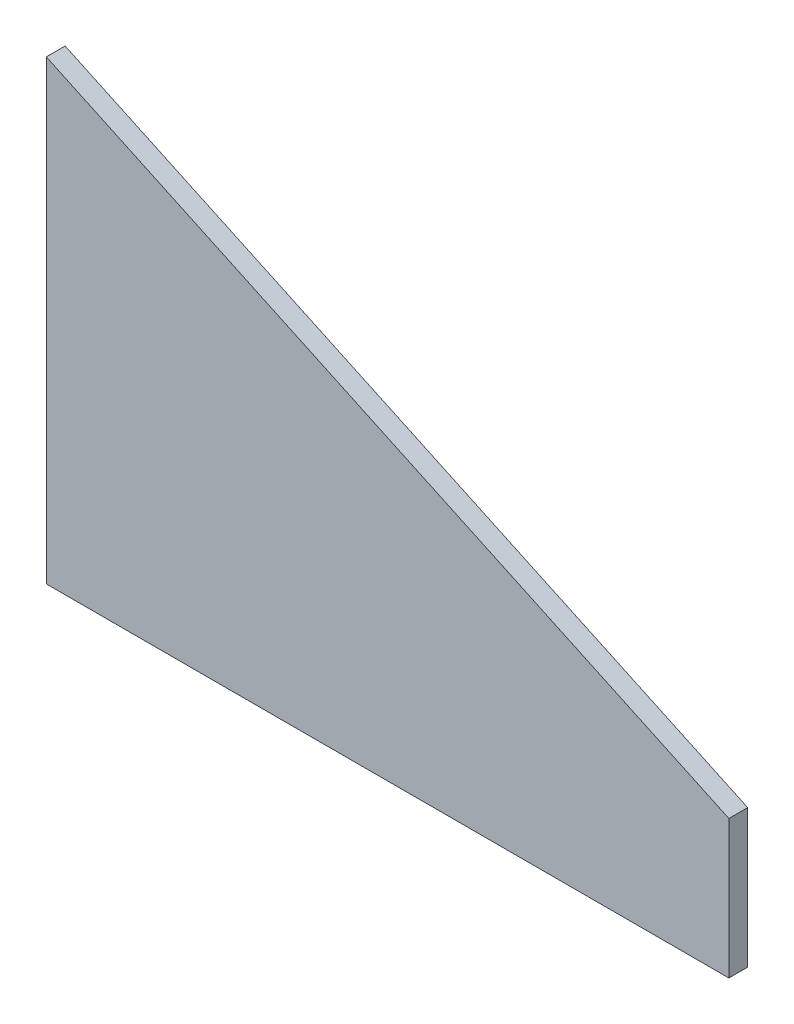
SolidWorks part; units mm, degrees
ref_plane "Front Plane" through (0, 0, 0) normal (0, 0, 1) x (1, 0, 0)
ref_plane "Top Plane" through (0, 0, 0) normal (0, 1, 0) x (1, 0, 0)
ref_plane "Right Plane" through (0, 0, 0) normal (1, 0, 0) x (0, 0, -1)
sketch "Sketch1" plane through (0, 0, 0) normal (0, 0, 1) x (1, 0, 0)
  line L0 (0, 0) -> (230.2022, 0)
  line L1 (230.2022, 0) -> (230.2022, 46.5901)
  line L2 (230.2022, 46.5901) -> (0, 153.9351)
  line L3 (0, 153.9351) -> (0, 0)
  line L4 (118.0552, 46.5901) -> (50118.0552, 46.5901) construction
  line L5 (48.3053, 131.41) -> (94.3457, 109.941) construction
  line L6 (94.3457, 109.941) -> (46.0404, 6.35) construction
  line L7 (46.0404, 6.35) -> (0, 27.819) construction
  line L8 (0, 27.819) -> (48.3053, 131.41) construction
  point P7 (-25.3116, 10.0219)
  point P12 (46.0404, 90.9538)
  point P13 (46.0404, 0)
  point P14 (46.0404, 73.325)
  point P15 (-42.5397, 18.0349)
  point P16 (-38.9338, 40.4715)
  point P17 (158.1874, 0)
  point P18 (0, 185.5078)
  point P19 (62.1589, 148.2151)
  point P20 (230.2022, 120.5219)
  point P21 (230.2022, 0)
  point P22 (0.0235, 261.2953)
  point P23 (4.7525, 273.6418)
  point P24 (0, 0)
  point P25 (0, 0)
  point P26 (230.2022, 249.2911)
  point P27 (48.3053, 9.0354)
  dimension "D1" = 25
  dimension "D2" = 114.3
  dimension "D3" = 50.8
  dimension "D4" = 254
  dimension "D5" = 6.35
extrude "Boss-Extrude1" add sketch "Sketch1" along normal blind 6.35
